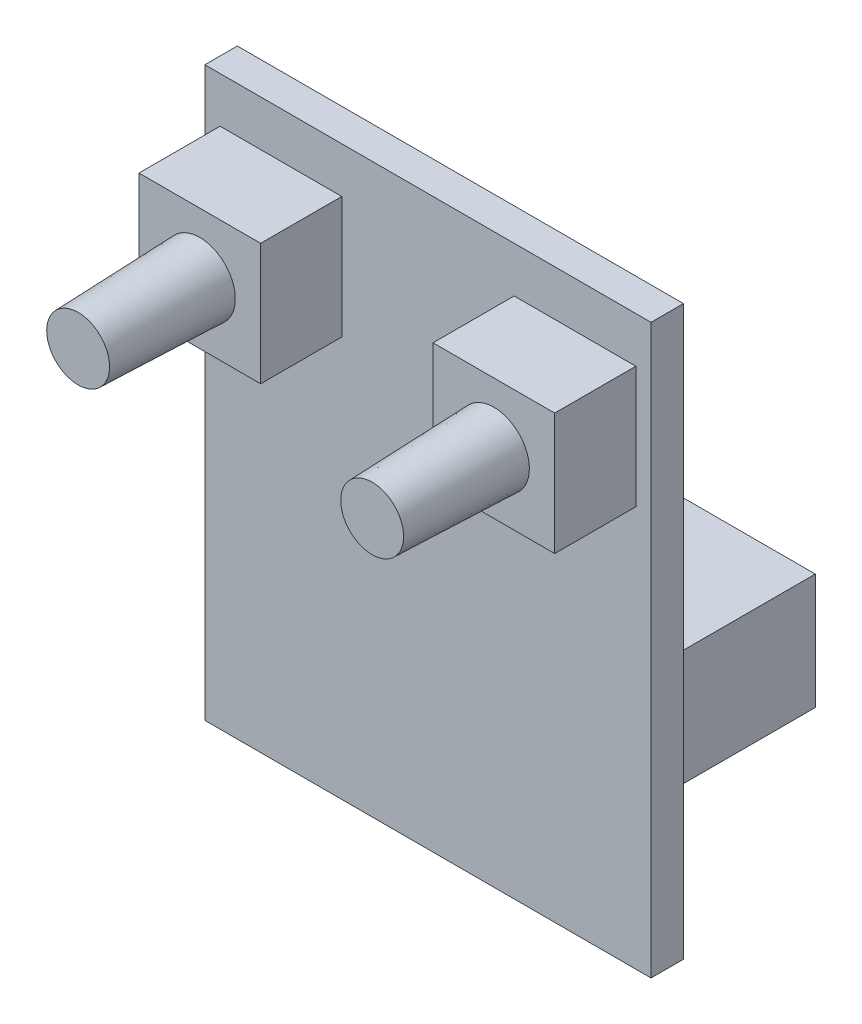
SolidWorks part; units mm, degrees
ref_plane "Front plane" through (0, 0, 0) normal (0, 0, 1) x (1, 0, 0)
ref_plane "Top plane" through (0, 0, 0) normal (0, 1, 0) x (1, 0, 0)
ref_plane "Right Plane" through (0, 0, 0) normal (1, 0, 0) x (0, 0, -1)
sketch "Sketch1" plane through (0, 0, 0) normal (0, 0, 1) x (1, 0, 0)
  line L1 (-11, 0) -> (11, 0)
  line L2 (-11, 0) -> (-11, 28)
  line L3 (-11, 28) -> (11, 28)
  line L4 (11, 0) -> (11, 28)
  dimension "D1" = 22
  dimension "D2" = 28
extrude "Boss-Extrude1" add sketch "Sketch1" along normal blind 1.6
sketch "Sketch2" plane through (0, 0, 1.6) normal (0, 0, 1) x (1, 0, 0)
  line L0 (-11, 0) -> (11, 0) construction
  line L5 (4.25, 25.75) -> (10.25, 25.75)
  line L6 (4.25, 25.75) -> (4.25, 19.75)
  line L7 (4.25, 19.75) -> (10.25, 19.75)
  line L8 (10.25, 25.75) -> (10.25, 19.75)
  point P0 (10.25, 22.75)
  point P3 (7.25, 19.75)
  dimension "D1" = 22.75
  dimension "D2" = 6
  dimension "D3" = 7.25
extrude "Boss-Extrude2" add sketch "Sketch2" along normal blind 4
sketch "Sketch3" plane through (0, 0, 0) normal (0, 0, -1) x (-1, 0, 0)
  line L1 (-10.5, 7) -> (2, 7)
  line L2 (-10.5, 7) -> (-10.5, 12.7)
  line L3 (-10.5, 12.7) -> (2, 12.7)
  line L4 (2, 7) -> (2, 12.7)
  line L6 (-10.5, 7) -> (10.5, 7) construction
  line L7 (3, 7) -> (10.5, 7)
  line L8 (3, 7) -> (3, 12.7)
  line L9 (3, 12.7) -> (10.5, 12.7)
  line L10 (10.5, 7) -> (10.5, 12.7)
  line L11 (11, 0) -> (-11, 0) construction
  point P13 (0, 7)
  point P16 (0, 0)
  dimension "D1" = 12.5
  dimension "D2" = 5.7
  dimension "D3" = 7
  dimension "D4" = 7.5
  dimension "D5" = 1
extrude "Boss-Extrude3" add sketch "Sketch3" along normal blind 7
ref_plane "Plane1" through (0, 0, 11.6) normal (0, 0, 1) x (1, 0, 0)
sketch "Sketch5" plane through (0, 0, 11.6) normal (0, 0, 1) x (1, 0, 0)
  line L0 (4.25, 19.75) -> (10.25, 25.75) construction
  circle A0 centre (7.25, 22.75) radius 1.55
  dimension "D1" = 3.1
sketch "Sketch6" plane through (0, 0, 5.6) normal (0, 0, 1) x (1, 0, 0)
  circle A0 centre (7.25, 22.75) radius 1.75
  dimension "D1" = 3.5
loft "Loft1" add profiles "Sketch5", "Sketch6"
mirror "Mirror1" about plane through (0, 0, 0) normal (1, 0, 0) of "Loft1", "Boss-Extrude2"
